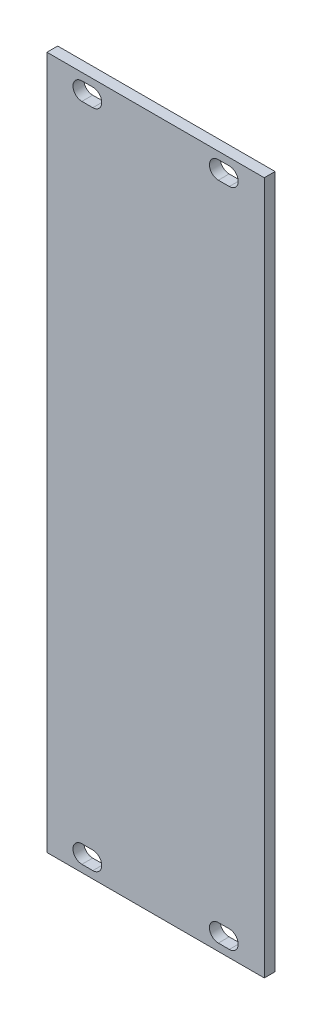
SolidWorks part; units mm, degrees
ref_plane "Front Plane" through (0, 0, 0) normal (0, 0, 1) x (1, 0, 0)
ref_plane "Top Plane" through (0, 0, 0) normal (0, 1, 0) x (1, 0, 0)
ref_plane "Right Plane" through (0, 0, 0) normal (1, 0, 0) x (0, 0, -1)
sketch "Sketch1" plane through (0, 0, 0) normal (0, 0, 1) x (1, 0, 0)
  line L0 (-12.65, 64.25) -> (-12.65, -64.25) construction
  line L1 (-20.15, 64.25) -> (20.15, 64.25)
  line L2 (-20.15, 64.25) -> (-20.15, -64.25)
  line L3 (-20.15, -64.25) -> (20.15, -64.25)
  line L4 (20.15, 64.25) -> (20.15, -64.25)
  line L5 (-20.15, 64.25) -> (20.15, -64.25) construction
  line L6 (-20.15, -64.25) -> (20.15, 64.25) construction
  line L7 (-20.15, 61.25) -> (20.15, 61.25) construction
  line L8 (-20.15, -61.25) -> (20.15, -61.25) construction
  line L9 (-13.666, -61.25) -> (-11.634, -61.25) construction
  line L10 (11.634, 61.25) -> (13.666, 61.25) construction
  line L11 (-13.666, -59.6) -> (-11.634, -59.6)
  line L12 (-13.666, -62.9) -> (-11.634, -62.9)
  line L13 (-13.666, 61.25) -> (-11.634, 61.25) construction
  line L14 (-13.666, 62.9) -> (-11.634, 62.9)
  line L15 (-13.666, 59.6) -> (-11.634, 59.6)
  line L16 (11.634, 62.9) -> (13.666, 62.9)
  line L17 (11.634, 59.6) -> (13.666, 59.6)
  line L18 (11.634, -61.25) -> (13.666, -61.25) construction
  line L19 (11.634, -59.6) -> (13.666, -59.6)
  line L20 (11.634, -62.9) -> (13.666, -62.9)
  line L21 (12.65, 64.25) -> (12.65, -64.25) construction
  arc A0 (-13.666, -59.6) -> (-13.666, -62.9) centre (-13.666, -61.25) ccw
  arc A1 (-11.634, -62.9) -> (-11.634, -59.6) centre (-11.634, -61.25) ccw
  arc A2 (-13.666, 62.9) -> (-13.666, 59.6) centre (-13.666, 61.25) ccw
  arc A3 (-11.634, 59.6) -> (-11.634, 62.9) centre (-11.634, 61.25) ccw
  arc A4 (11.634, 62.9) -> (11.634, 59.6) centre (11.634, 61.25) ccw
  arc A5 (13.666, 59.6) -> (13.666, 62.9) centre (13.666, 61.25) ccw
  arc A6 (11.634, -59.6) -> (11.634, -62.9) centre (11.634, -61.25) ccw
  arc A7 (13.666, -62.9) -> (13.666, -59.6) centre (13.666, -61.25) ccw
  point P0 (0, 0)
  point P8 (12.65, 61.25)
  point P18 (-12.65, -61.25)
  point P24 (-12.65, 61.25)
  point P34 (12.65, -61.25)
  point P42 (0, 0)
  point P43 (0, 0)
  dimension "D6" = 1.65
  dimension "D7" = 1.65
  dimension "D11" = 1.65
  dimension "D13" = 1.65
  dimension "D1" = 128.5
  dimension "D2" = 40.3
  dimension "D3" = 7.5
  dimension "D4" = 3
  dimension "D8" = 2.032
  dimension "D9" = 2.032
  dimension "D10" = 7.5
  dimension "D12" = 2.032
  dimension "D14" = 2.032
  dimension "D5" = 3
extrude "Boss-Extrude1" add sketch "Sketch1" along normal blind 2
